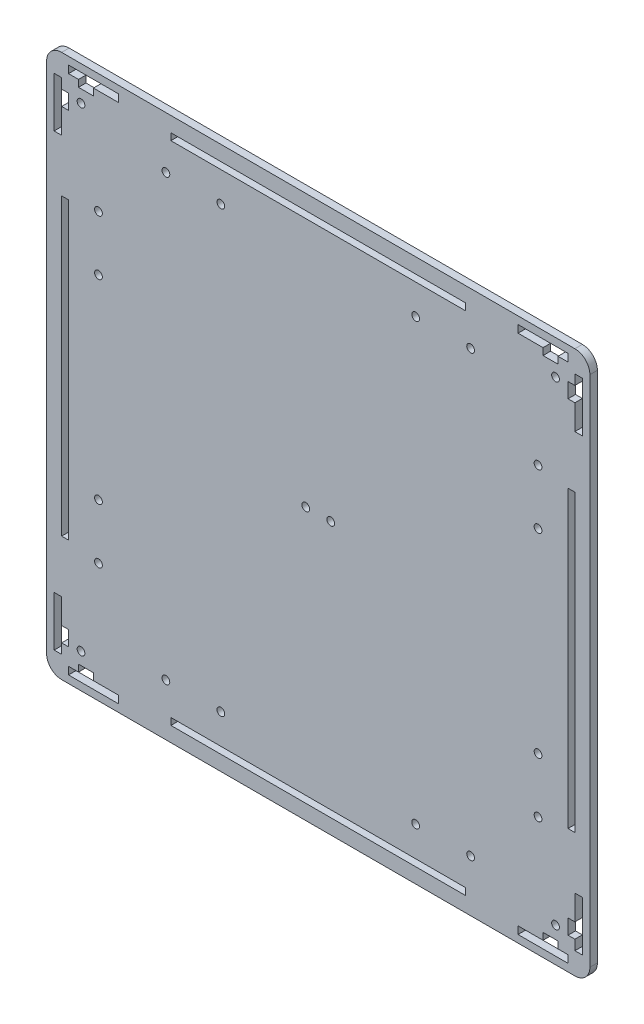
SolidWorks part; units mm, degrees
ref_plane "前视基准面" through (0, 0, 0) normal (0, 0, 1) x (1, 0, 0)
ref_plane "上视基准面" through (0, 0, 0) normal (0, 1, 0) x (1, 0, 0)
ref_plane "右视基准面" through (0, 0, 0) normal (1, 0, 0) x (0, 0, -1)
sketch "草图1" plane through (0, 0, 0) normal (0, 0, 1) x (1, 0, 0)
  line L0 (0, 202.75) -> (0, 205.75)
  line L1 (4, 0) -> (10, 0)
  line L2 (0, 4) -> (0, 10)
  line L3 (4, 200) -> (10, 200)
  line L4 (200, 4) -> (200, 10)
  line L7 (0, -2.75) -> (4, -2.75)
  line L16 (-2.75, 0) -> (-2.75, 4)
  line L19 (0, 202.75) -> (4, 202.75)
  line L21 (0, 205.75) -> (20, 205.75)
  line L22 (20, 205.75) -> (20, 202.75)
  line L24 (200, 202.75) -> (200, 205.75)
  line L25 (202.75, 200) -> (205.75, 200)
  line L26 (200, 205.75) -> (180, 205.75)
  line L27 (180, 205.75) -> (180, 202.75)
  line L28 (200, -2.75) -> (200, -5.75)
  line L30 (200, 196) -> (200, 190)
  line L32 (202.75, 200) -> (202.75, 196)
  line L33 (202.75, 0) -> (205.75, 0)
  line L34 (205.75, 0) -> (205.75, 20)
  line L35 (-2.75, 0) -> (-5.75, 0)
  line L36 (205.75, 20) -> (202.75, 20)
  line L39 (0, -2.75) -> (0, -5.75)
  line L40 (0, -5.75) -> (20, -5.75)
  line L41 (20, -5.75) -> (20, -2.75)
  line L42 (200, -5.75) -> (180, -5.75)
  line L43 (180, -5.75) -> (180, -2.75)
  line L44 (196, 0) -> (190, 0)
  line L49 (159, 0) -> (159, -2.75)
  line L50 (180, -2.75) -> (190, -2.75)
  line L56 (41, 0) -> (41, -2.75)
  line L57 (41, -2.75) -> (159, -2.75)
  line L60 (208.75, -2.75) -> (208.75, 202.75)
  line L62 (202.75, 208.75) -> (-2.75, 208.75)
  line L64 (-8.75, 202.75) -> (-8.75, -2.75)
  line L66 (-2.75, -8.75) -> (202.75, -8.75)
  line L70 (200, 41) -> (202.75, 41)
  line L71 (202.75, 20) -> (202.75, 10)
  line L73 (205.75, 200) -> (205.75, 180)
  line L74 (205.75, 180) -> (202.75, 180)
  line L80 (200, 159) -> (202.75, 159)
  line L81 (202.75, 159) -> (202.75, 41)
  line L82 (196, 200) -> (190, 200)
  line L87 (159, 200) -> (159, 202.75)
  line L88 (180, 202.75) -> (190, 202.75)
  line L92 (41, 200) -> (41, 202.75)
  line L93 (41, 202.75) -> (159, 202.75)
  line L94 (-2.75, 200) -> (-5.75, 200)
  line L95 (-5.75, 200) -> (-5.75, 180)
  line L96 (-5.75, 180) -> (-2.75, 180)
  line L97 (0, 196) -> (0, 190)
  line L102 (0, 159) -> (-2.75, 159)
  line L103 (-2.75, 180) -> (-2.75, 190)
  line L104 (-5.75, 0) -> (-5.75, 20)
  line L105 (-5.75, 20) -> (-2.75, 20)
  line L112 (0, 41) -> (-2.75, 41)
  line L113 (-2.75, 41) -> (-2.75, 159)
  line L147 (196, -2.75) -> (200, -2.75)
  line L167 (202.75, 4) -> (202.75, 0)
  line L189 (41, 0) -> (159, 0)
  line L193 (0, 159) -> (0, 41)
  line L194 (-2.75, 196) -> (-2.75, 200)
  line L195 (10, 202.75) -> (20, 202.75)
  line L199 (41, 200) -> (159, 200)
  line L204 (196, 202.75) -> (200, 202.75)
  line L205 (202.75, 190) -> (202.75, 180)
  line L211 (-2.75, 10) -> (-2.75, 20)
  line L226 (10, -2.75) -> (20, -2.75)
  line L227 (190, 0) -> (190, -2.75)
  line L230 (196, 200) -> (196, 202.75)
  line L231 (202.75, 10) -> (200, 10)
  line L233 (200, 41) -> (200, 159)
  line L234 (202.75, 190) -> (200, 190)
  line L237 (190, 202.75) -> (190, 200)
  line L239 (200, 196) -> (202.75, 196)
  line L241 (10, 202.75) -> (10, 200)
  line L244 (200, 4) -> (202.75, 4)
  line L245 (-2.75, 190) -> (0, 190)
  line L248 (10, -2.75) -> (10, 0)
  line L250 (196, 0) -> (196, -2.75)
  line L251 (-2.75, 10) -> (0, 10)
  line L254 (0, 196) -> (-2.75, 196)
  line L256 (4, 200) -> (4, 202.75)
  line L258 (4, -2.75) -> (4, 0)
  line L260 (0, 4) -> (-2.75, 4)
  circle A16 centre (5, 195) radius 1.55
  circle A17 centre (195, 195) radius 1.55
  circle A18 centre (195, 5) radius 1.55
  circle A19 centre (5, 5) radius 1.55
  circle A21 centre (95, 100) radius 1.55
  circle A22 centre (105, 100) radius 1.55
  circle A23 centre (39, 12) radius 1.55
  circle A24 centre (61, 12) radius 1.55
  circle A25 centre (139, 12) radius 1.55
  circle A26 centre (161, 12) radius 1.55
  circle A27 centre (188, 39) radius 1.55
  circle A28 centre (188, 61) radius 1.55
  circle A29 centre (188, 161) radius 1.55
  circle A30 centre (188, 139) radius 1.55
  circle A31 centre (39, 188) radius 1.55
  circle A32 centre (61, 188) radius 1.55
  circle A33 centre (139, 188) radius 1.55
  circle A34 centre (161, 188) radius 1.55
  circle A35 centre (12, 161) radius 1.55
  circle A36 centre (12, 139) radius 1.55
  circle A37 centre (12, 61) radius 1.55
  circle A38 centre (12, 39) radius 1.55
  arc A39 (208.75, -2.75) -> (202.75, -8.75) centre (202.75, -2.75) cw
  arc A40 (208.75, 202.75) -> (202.75, 208.75) centre (202.75, 202.75) ccw
  arc A41 (-2.75, 208.75) -> (-8.75, 202.75) centre (-2.75, 202.75) ccw
  arc A42 (-2.75, -8.75) -> (-8.75, -2.75) centre (-2.75, -2.75) cw
extrude "凸台-拉伸2" add sketch "草图1" along normal blind 3
